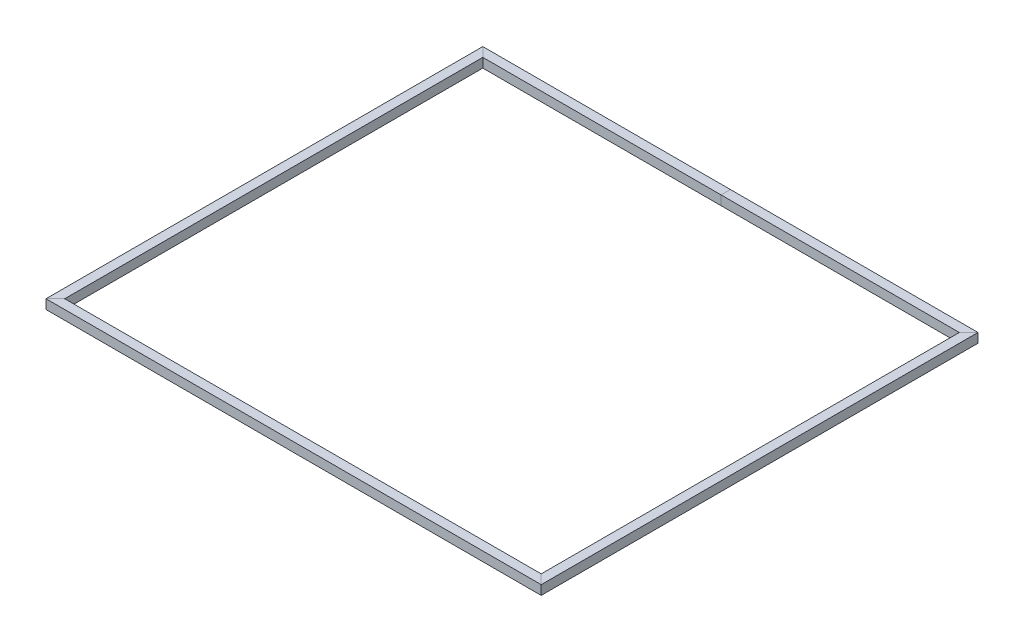
SolidWorks part; units mm, degrees
ref_plane "Front Plane" through (0, 0, 0) normal (0, 0, 1) x (1, 0, 0)
ref_plane "Top Plane" through (0, 0, 0) normal (0, 1, 0) x (1, 0, 0)
ref_plane "Right Plane" through (0, 0, 0) normal (1, 0, 0) x (0, 0, -1)
sketch "Sketch1" plane through (0, 0, 0) normal (1, 0, 0) x (0, 0, -1)
  line L1 (1136.65, 25.4) -> (1187.45, 25.4)
  line L2 (1136.65, 25.4) -> (1136.65, -25.4)
  line L3 (1136.65, -25.4) -> (1187.45, -25.4)
  line L4 (1187.45, 25.4) -> (1187.45, -25.4)
  line L5 (1136.65, 25.4) -> (1187.45, -25.4) construction
  line L6 (1136.65, -25.4) -> (1187.45, 25.4) construction
  line L7 (1138.2375, 23.8125) -> (1185.8625, 23.8125)
  line L8 (1138.2375, 23.8125) -> (1138.2375, -23.8125)
  line L9 (1138.2375, -23.8125) -> (1185.8625, -23.8125)
  line L10 (1185.8625, 23.8125) -> (1185.8625, -23.8125)
  line L11 (1138.2375, 23.8125) -> (1185.8625, -23.8125) construction
  line L12 (1138.2375, -23.8125) -> (1185.8625, 23.8125) construction
  point P0 (1162.05, 0)
  point P5 (1162.05, 0)
  point P10 (0, 0)
  dimension "D1" = 50.8
  dimension "D2" = 50.8
  dimension "D3" = 47.625
  dimension "D4" = 1162.05
sketch "Sketch2" plane through (0, 0, 0) normal (0, 1, 0) x (1, 0, 0)
  line L1 (1320.8, -1162.05) -> (-1320.8, -1162.05)
  line L2 (1320.8, -1162.05) -> (1320.8, 1162.05)
  line L3 (1320.8, 1162.05) -> (-1320.8, 1162.05)
  line L4 (-1320.8, -1162.05) -> (-1320.8, 1162.05)
  line L5 (1320.8, -1162.05) -> (-1320.8, 1162.05) construction
  line L6 (1320.8, 1162.05) -> (-1320.8, -1162.05) construction
  point P0 (0, 0)
  dimension "D1" = 2324.1
  dimension "D2" = 2641.6
sweep "Sweep1" add profiles "Sketch1" path "Sketch2"
